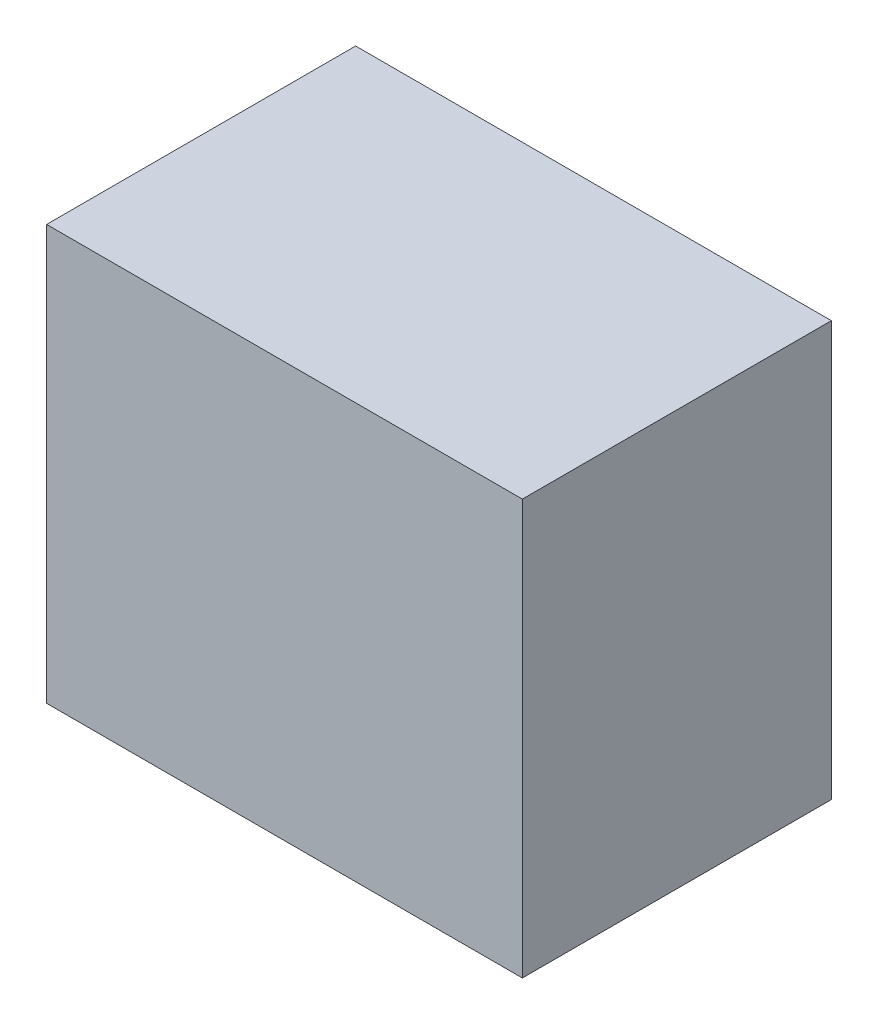
SolidWorks part; units mm, degrees
material "A286 Iron Base Superalloy"
ref_plane "Front Plane" through (0, 0, 0) normal (0, 0, 1) x (1, 0, 0)
ref_plane "Top Plane" through (0, 0, 0) normal (0, 1, 0) x (1, 0, 0)
ref_plane "Right Plane" through (0, 0, 0) normal (1, 0, 0) x (0, 0, -1)
sketch "Sketch1" plane through (0, 0, 0) normal (0, 1, 0) x (1, 0, 0)
  line L1 (0, 0) -> (11.7, 0)
  line L2 (0, 0) -> (0, 7.6)
  line L3 (0, 7.6) -> (11.7, 7.6)
  line L4 (11.7, 0) -> (11.7, 7.6)
  dimension "D1" = 7.6
  dimension "D2" = 11.7
extrude "Boss-Extrude1" add sketch "Sketch1" along normal blind 10.2
